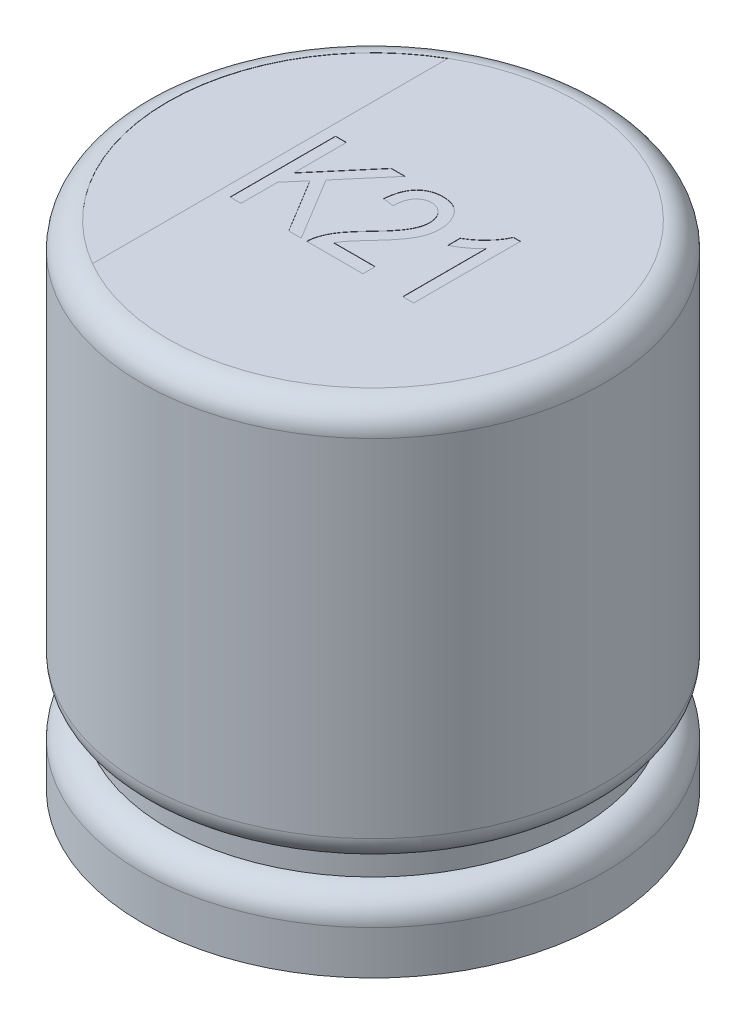
SolidWorks part; units mm, degrees
material "1060-H16"
ref_plane "Front Plane" through (0, 0, 0) normal (0, 0, 1) x (1, 0, 0)
ref_plane "Top Plane" through (0, 0, 0) normal (0, 1, 0) x (1, 0, 0)
ref_plane "Right Plane" through (0, 0, 0) normal (1, 0, 0) x (0, 0, -1)
sketch "Sketch1" plane through (0, 0, 0) normal (0, 1, 0) x (1, 0, 0)
  circle A0 centre (0, 0) radius 9
  dimension "D1" = 18
extrude "Boss-Extrude1" add sketch "Sketch1" along normal blind 19.2
fillet "Fillet1" radius 1 1 edges at (0, 19.2, 9)
sketch "Sketch2" plane through (0, 0, 0) normal (0, 0, 1) x (1, 0, 0)
  line L0 (-9, 18.2) -> (-9, 0) construction
  line L1 (-9, 4.7) -> (-8, 4.7) construction
  line L2 (-9, 4.7) -> (-9, 1.7)
  line L3 (-9, 1.7) -> (-8, 1.7) construction
  line L4 (-8, 4.7) -> (-8, 1.7) construction
  line L5 (8, 19.2) -> (-8, 19.2) construction
  line L6 (-8, 3.7) -> (-8, 2.7)
  arc A0 (-9, 4.7) -> (-8, 3.7) centre (-8, 4.7) ccw
  arc A1 (-8, 2.7) -> (-9, 1.7) centre (-8, 1.7) ccw
  point P8 (-9, 3.2)
  dimension "D1" = 1
  dimension "D2" = 16
  dimension "D3" = 3
ref_axis "Axis1" through (0, -0.75, 0) along (0, 1, 0)
revolve "Cut-Revolve1" cut sketch "Sketch2" angle 360 about axis through (0, -0.75, 0) along (0, 1, 0)
sketch "Sketch3" plane through (0, 19.2, 0) normal (0, 1, 0) x (1, 0, 0)
  line L0 (-4, 6.9282) -> (-4, -6.9282)
  line L1 (0, -9.9) -> (0, 9.9) construction
  arc A0 (-4, 6.9282) -> (-4, -6.9282) centre (0, 0) ccw
  circle A1 centre (0, 0) radius 8 construction
  dimension "D1" = 4
extrude "Cut-Extrude1" cut sketch "Sketch3" against normal blind 0.01
sketch "Sketch4" plane through (0, 19.2, 0) normal (0, 1, 0) x (1, 0, 0)
  line L0 (-3.9421, -2) -> (3.9421, -2) construction
  line L1 (0, -9.9) -> (0, 9.9) construction
  line L2 (-9.9, 0) -> (9.9, 0) construction
  text T0 "K21\r\n" font "Arial Narrow" height in points 16
  point P2 (0, -2)
  point P8 (-6.0294, -2)
  point P9 (7.0224, -2)
  point P10 (4.7805, -2)
  point P11 (0, 0)
  point P12 (3.9421, -2)
  dimension "D1" = 2
extrude "Cut-Extrude2" cut sketch "Sketch4" against normal blind 0.01
